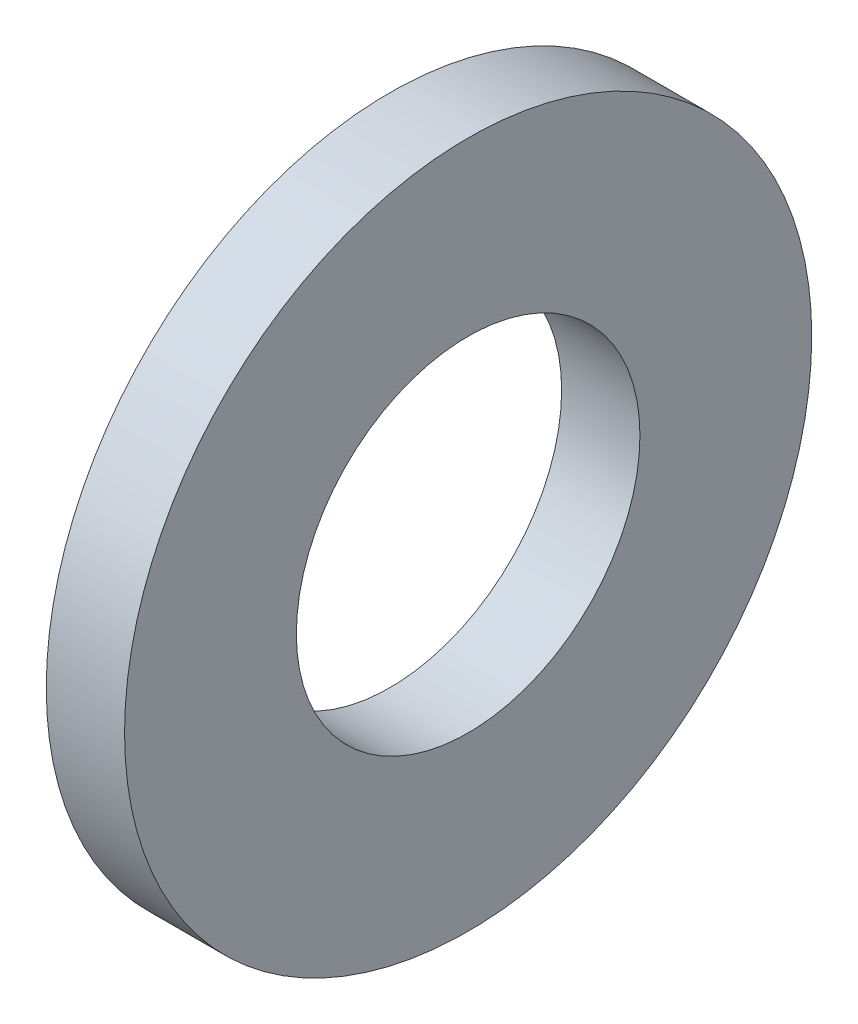
SolidWorks part; units mm, degrees
ref_plane "Front Plane" through (0, 0, 0) normal (0, 0, 1) x (1, 0, 0)
ref_plane "Top Plane" through (0, 0, 0) normal (0, 1, 0) x (1, 0, 0)
ref_plane "Right Plane" through (0, 0, 0) normal (1, 0, 0) x (0, 0, -1)
sketch "Sketch1" plane through (0, 0, 0) normal (1, 0, 0) x (0, 0, -1)
  circle A0 centre (0, 0) radius 13.4874
  circle A1 centre (0, 0) radius 6.7437
  dimension "OD" = 26.9748
  dimension "ID" = 13.4874
extrude "Boss-Extrude1" add sketch "Sketch1" along normal blind 3.0734
